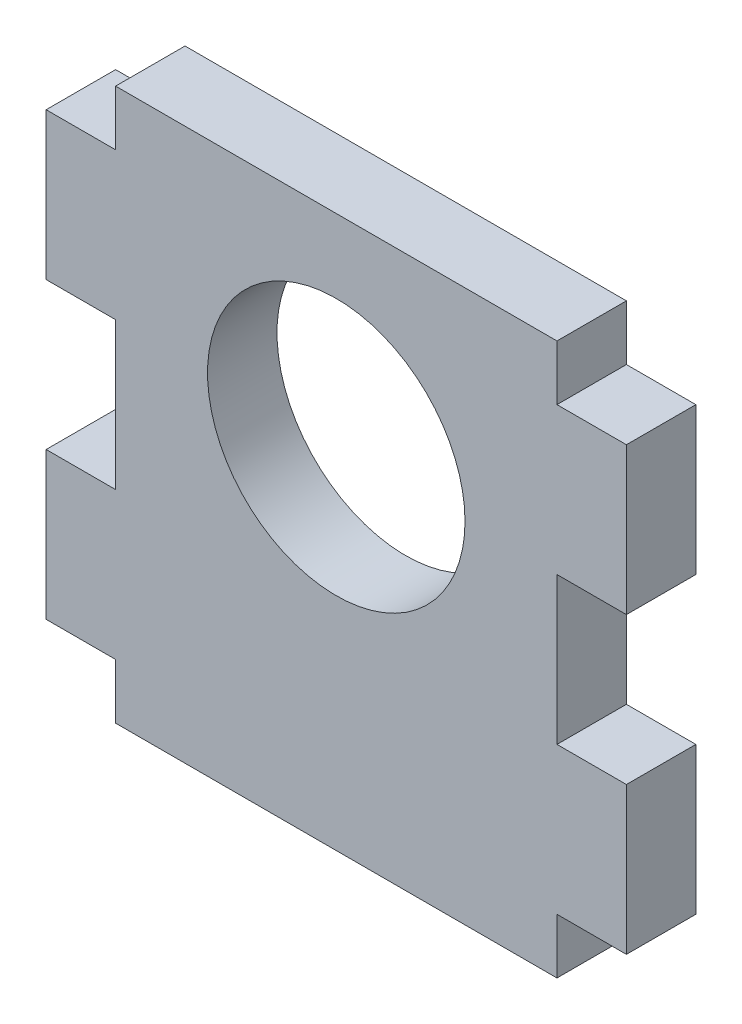
SolidWorks part; units mm, degrees
ref_plane "Front Plane" through (0, 0, 0) normal (0, 0, 1) x (1, 0, 0)
ref_plane "Top Plane" through (0, 0, 0) normal (0, 1, 0) x (1, 0, 0)
ref_plane "Right Plane" through (0, 0, 0) normal (1, 0, 0) x (0, 0, -1)
sketch "Sketch1" plane through (0, 0, 0) normal (0, 0, 1) x (1, 0, 0)
  line L0 (0, 19.05) -> (0, -31.75) construction
  line L1 (19.05, 19.05) -> (-19.05, 19.05)
  line L2 (19.05, 19.05) -> (19.05, 12.7)
  line L3 (19.05, -31.75) -> (-19.05, -31.75)
  line L4 (-19.05, 19.05) -> (-19.05, 12.7)
  line L5 (-19.05, -6.35) -> (19.05, -6.35) construction
  line L6 (-25.0444, -25.4) -> (-25.0444, -12.7)
  line L7 (-19.05, 12.7) -> (-25.0444, 12.7)
  line L8 (-19.05, -25.4) -> (-19.05, -31.75)
  line L9 (-19.05, 0) -> (-25.0444, 0)
  line L10 (-25.0444, 12.7) -> (-25.0444, 0)
  line L11 (-19.05, -12.7) -> (-25.0444, -12.7)
  line L12 (19.05, -25.4) -> (19.05, -31.75)
  line L13 (-19.05, -25.4) -> (-25.0444, -25.4)
  line L14 (19.05, -25.4) -> (25.0444, -25.4)
  line L15 (19.05, 0) -> (19.05, -12.7)
  line L16 (19.05, -12.7) -> (25.0444, -12.7)
  line L17 (25.0444, 12.7) -> (25.0444, 0)
  line L18 (19.05, 0) -> (25.0444, 0)
  line L20 (19.05, 12.7) -> (25.0444, 12.7)
  line L21 (25.0444, -25.4) -> (25.0444, -12.7)
  line L22 (-19.05, 0) -> (-19.05, -12.7)
  circle A0 centre (0, 0) radius 11.1125
  dimension "D1" = 22.225
  dimension "D2" = 19.05
  dimension "D3" = 38.1
  dimension "D4" = 50.8
  dimension "D5" = 5.9944
  dimension "D6" = 12.7
  dimension "D7" = 6.35
extrude "Boss-Extrude1" add sketch "Sketch1" along normal blind 5.9944
sketch "Sketch2" plane through (0, 0, 5.9944) normal (0, 0, 1) x (1, 0, 0)
  line L0 (19.05, -31.75) -> (19.05, -25.4) construction
  line L1 (-19.05, -31.75) -> (19.05, -31.75)
  line L2 (-19.05, -31.75) -> (-19.05, -30.1625)
  line L3 (-19.05, -30.1625) -> (19.05, -30.1625)
  line L4 (19.05, -31.75) -> (19.05, -30.1625)
  line L5 (19.05, 12.7) -> (19.05, 19.05) construction
  line L6 (-19.05, 19.05) -> (19.05, 19.05)
  line L7 (-19.05, 19.05) -> (-19.05, 17.4625)
  line L8 (-19.05, 17.4625) -> (19.05, 17.4625)
  line L9 (19.05, 19.05) -> (19.05, 17.4625)
  dimension "D1" = 1.5875
  dimension "D2" = 1.5875
extrude "Cut-Extrude1" cut sketch "Sketch2" against normal through all
